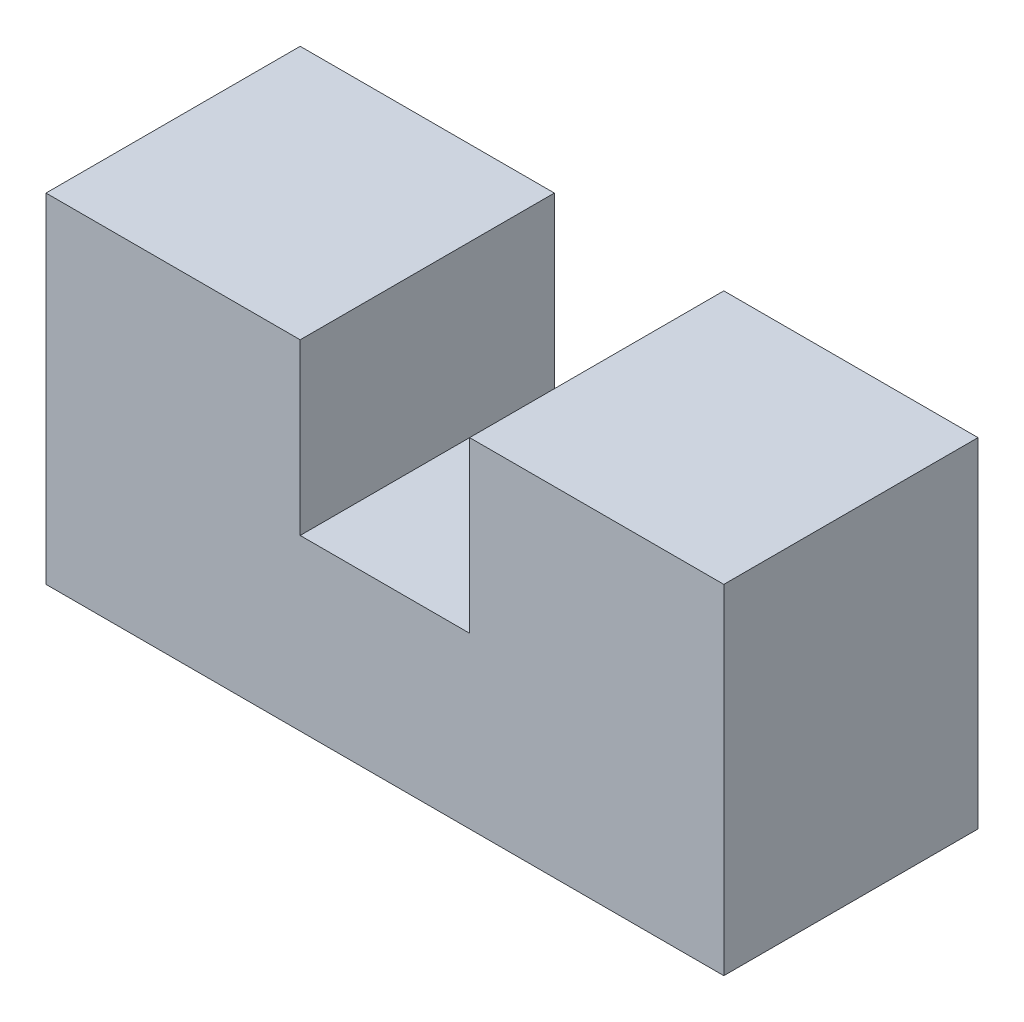
SolidWorks part; units mm, degrees
ref_plane "Front Plane" through (0, 0, 0) normal (0, 0, 1) x (1, 0, 0)
ref_plane "Top Plane" through (0, 0, 0) normal (0, 1, 0) x (1, 0, 0)
ref_plane "Right Plane" through (0, 0, 0) normal (1, 0, 0) x (0, 0, -1)
sketch "Sketch2" plane through (0, 0, 0) normal (0, 0, 1) x (1, 0, 0)
  line L0 (0, 0) -> (0, -40)
  line L1 (0, -40) -> (80, -40)
  line L2 (80, -40) -> (80, 0)
  line L3 (80, 0) -> (50, 0)
  line L4 (50, 0) -> (50, -20)
  line L5 (50, -20) -> (30, -20)
  line L6 (30, -20) -> (30, 0)
  line L7 (30, 0) -> (0, 0)
  point P9 (50, 0)
  dimension "D1" = 40
  dimension "D2" = 80
  dimension "D3" = 30
  dimension "D4" = 20
  dimension "D5" = 20
extrude "Boss-Extrude1" add sketch "Sketch2" along normal mid plane 30
